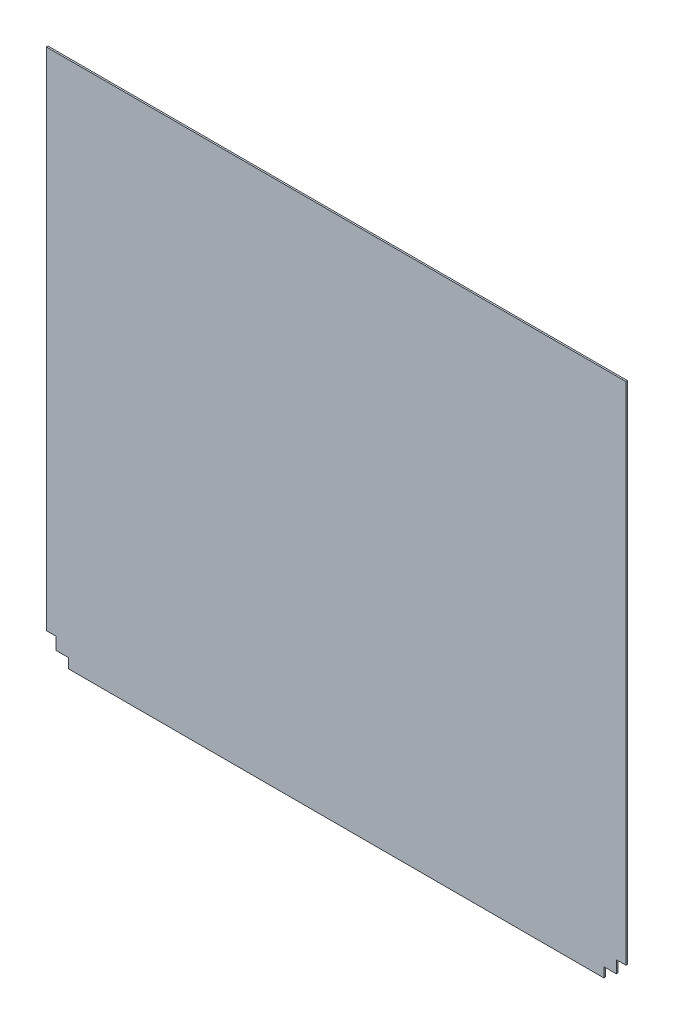
SolidWorks part; units mm, degrees
ref_plane "Front Plane" through (0, 0, 0) normal (0, 0, 1) x (1, 0, 0)
ref_plane "Top Plane" through (0, 0, 0) normal (0, 1, 0) x (1, 0, 0)
ref_plane "Right Plane" through (0, 0, 0) normal (1, 0, 0) x (0, 0, -1)
sketch "Sketch1" plane through (0, 0, 0) normal (0, 0, 1) x (1, 0, 0)
  line L0 (0, 34.544) -> (15.24, 34.544)
  line L1 (0, 0) -> (907.001, 0)
  line L2 (0, 0) -> (0, 825.5)
  line L3 (0, 825.5) -> (907.001, 825.5)
  line L4 (907.001, 0) -> (907.001, 825.5)
  line L5 (0, 0) -> (914.4, 0) construction
  line L6 (0, 0) -> (0, 914.4) construction
  line L7 (0, 914.4) -> (914.4, 914.4) construction
  line L8 (914.4, 0) -> (914.4, 914.4) construction
  line L9 (15.24, 34.544) -> (15.24, 15.24)
  line L10 (15.24, 15.24) -> (34.544, 15.24)
  line L11 (34.544, 15.24) -> (34.544, 0)
  line L12 (907.001, 34.544) -> (891.761, 34.544)
  line L13 (891.761, 34.544) -> (891.761, 15.24)
  line L14 (891.761, 15.24) -> (872.457, 15.24)
  line L15 (872.457, 15.24) -> (872.457, 0)
  dimension "D1" = 825.5
  dimension "D2" = 907.001
  dimension "D3" = 914.4
  dimension "D4" = 914.4
  dimension "D5" = 15.24
  dimension "D6" = 15.24
  dimension "D7" = 34.544
  dimension "D8" = 34.544
  dimension "D9" = 15.24
  dimension "D10" = 15.24
  dimension "D11" = 34.544
  dimension "D12" = 34.544
extrude "Boss-Extrude1" add sketch "Sketch1" along normal blind 2.54 contours L15 L14 L13 L12 L4 L3 L2 L0 L9 L10 L11 L1
